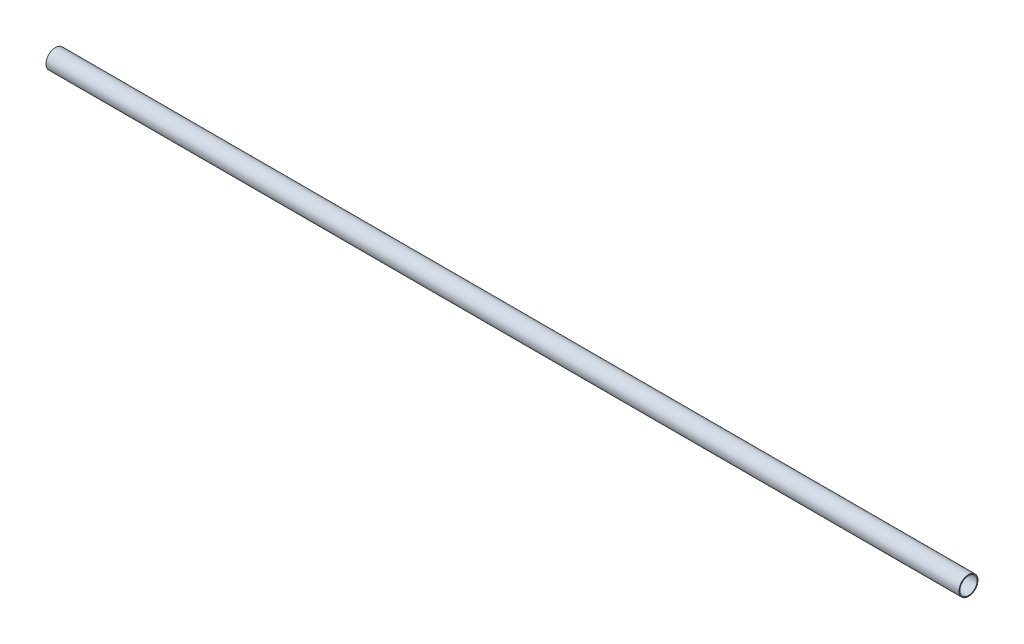
SolidWorks part; units mm, degrees
ref_plane "Front" through (0, 0, 0) normal (0, 0, 1) x (1, 0, 0)
ref_plane "Top" through (0, 0, 0) normal (0, 1, 0) x (1, 0, 0)
ref_plane "Right" through (0, 0, 0) normal (1, 0, 0) x (0, 0, -1)
sketch "Sketch1" plane through (0, 0, 0) normal (1, 0, 0) x (0, 0, -1)
  circle A0 centre (0, 0) radius 9.525
  circle A1 centre (0, 0) radius 8.636
  point P4 (9.525, 0)
  point P5 (8.636, 0)
  dimension "OD" = 19.05
  dimension "ID" = 17.272
  dimension "Wall" = 0.889
sketch "Sketch4" plane through (0, 0, 0) normal (1, 0, 0) x (0, 0, -1)
  circle A0 centre (0, 0) radius 9.525 construction
  circle A1 centre (0, 0) radius 9.525
  circle A2 centre (0, 0) radius 8.636 construction
  circle A3 centre (0, 0) radius 8.636
extrude "Boss-Extrude1" add sketch "Sketch4" along normal mid plane 914.4
sketch "Sketch2" plane through (0, 0, 0) normal (0, 0, 1) x (1, 0, 0)
  line L0 (-457.2, 0) -> (457.2, 0) construction
  line L2 (-457.2, 9.525) -> (-457.2, -9.525) construction
  point P5 (-408.94, 0)
  point P6 (408.94, 0)
  dimension "D1" = 48.26
  dimension "D2" = 48.26
equation "\"D1@Sketch2\"=.9+(\"length@Boss-Extrude1\"/36)"
equation "\"D2@Sketch2\"=\"D1@Sketch2\""
